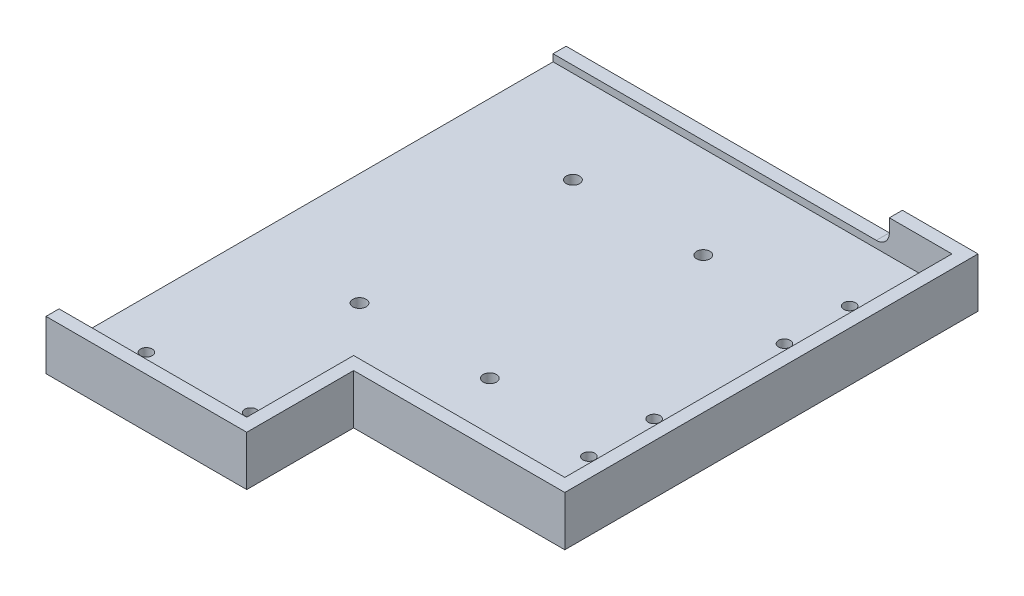
SolidWorks part; units mm, degrees
ref_plane "Front Plane" through (0, 0, 0) normal (0, 0, 1) x (1, 0, 0)
ref_plane "Top Plane" through (0, 0, 0) normal (0, 1, 0) x (1, 0, 0)
ref_plane "Right Plane" through (0, 0, 0) normal (1, 0, 0) x (0, 0, -1)
sketch "Sketch1" plane through (0, 0, 0) normal (0, 1, 0) x (1, 0, 0)
  line L1 (0, 0) -> (158, 0)
  line L2 (0, 0) -> (0, -199.5)
  line L3 (0, -199.5) -> (158, -199.5)
  line L4 (158, 0) -> (158, -199.5)
  dimension "D1" = 158
  dimension "D2" = 199.5
extrude "Boss-Extrude1" add sketch "Sketch1" along normal blind 6.35
sketch "Sketch2" plane through (0, 6.35, 0) normal (0, 1, 0) x (1, 0, 0)
  line L0 (0, -199.5) -> (158, -199.5) construction
  line L1 (158, -199.5) -> (77, -199.5)
  line L2 (158, -199.5) -> (158, -158.5)
  line L3 (158, -158.5) -> (77, -158.5)
  line L4 (77, -199.5) -> (77, -158.5)
  dimension "D1" = 81
  dimension "D2" = 41
extrude "Cut-Extrude1" cut sketch "Sketch2" against normal through all
sketch "Sketch3" plane through (0, 6.35, 0) normal (0, 1, 0) x (1, 0, 0)
  line L0 (0, 0) -> (0, -5)
  line L1 (0, 0) -> (0, -199.5) construction
  line L2 (0, -5) -> (153, -5)
  line L3 (153, -5) -> (153, -153.5)
  line L4 (153, -153.5) -> (72, -153.5)
  line L5 (72, -153.5) -> (72, -194.5)
  line L6 (0, -199.5) -> (77, -199.5) construction
  line L7 (77, -158.5) -> (77, -199.5) construction
  line L8 (158, -158.5) -> (77, -158.5) construction
  line L9 (158, -158.5) -> (158, 0) construction
  line L10 (158, 0) -> (0, 0) construction
  line L11 (77, -158.5) -> (77, -199.5)
  line L12 (158, -158.5) -> (77, -158.5)
  line L13 (158, -158.5) -> (158, 0)
  line L14 (158, 0) -> (0, 0)
  line L15 (72, -199.5) -> (77, -199.5)
  line L17 (0, -194.5) -> (72, -194.5)
  line L18 (0, -194.5) -> (0, -199.5)
  line L19 (0, -199.5) -> (72, -199.5)
  dimension "D1" = 5
  dimension "D2" = 5
  dimension "D3" = 5
  dimension "D4" = 5
  dimension "D5" = 5
extrude "Boss-Extrude2" add sketch "Sketch3" along normal blind 12.7
sketch "Sketch4" plane through (0, 0, 0) normal (0, -1, 0) x (1, 0, 0)
  line L0 (0, 179.5) -> (77, 179.5) construction
  line L1 (0, 0) -> (0, 199.5) construction
  line L2 (77, 158.5) -> (77, 199.5) construction
  line L3 (0, 199.5) -> (77, 199.5) construction
  line L4 (38.5, 179.5) -> (38.5, 188.5903) construction
  line L5 (138, 158.5) -> (138, 0) construction
  line L6 (158, 158.5) -> (77, 158.5) construction
  line L7 (158, 0) -> (0, 0) construction
  line L8 (158, 158.5) -> (158, 0) construction
  line L9 (138, 79.25) -> (152.6176, 79.25) construction
  point P8 (18.5, 179.5)
  point P11 (58.5, 179.5)
  point P20 (138, 129.25)
  point P21 (138, 104.25)
  point P22 (138, 29.25)
  point P23 (138, 79.25)
  point P24 (138, 54.25)
  dimension "D1" = 20
  dimension "D2" = 40
  dimension "D3" = 20
  dimension "D4" = 25
  dimension "D5" = 25
hole_wizard "M4 Clearance Hole1" positions "Sketch4" profile "Sketch5" hole size "M4" standard "ANSI Metric" end condition up to next
sketch "Sketch5" plane through (138, 0, 54.25) normal (1, 0, 0) x (0, 0, -1)
  line L0 (0, 0) -> (0, 6.35)
  line L1 (0, 6.35) -> (2.25, 6.35)
  line L2 (2.25, 6.35) -> (2.25, 0)
  line L5 (2.25, 0) -> (0, 0)
  line L11 (0, -6.35) -> (0, 107.95) construction
  dimension "Thru Hole Dia." = 4.5
  dimension "Thru Hole Depth" = 6.35
sketch "Sketch7" plane through (0, 0, 0) normal (0, 0, -1) x (-1, 0, 0)
  line L0 (-79, 19.05) -> (-79, 4.7647) construction
  line L1 (-158, 19.05) -> (0, 19.05) construction
  line L2 (-158, 19.05) -> (-158, 0) construction
  line L3 (-129, 19.05) -> (0, 19.05)
  line L4 (-129, 19.05) -> (-129, 9.05)
  line L5 (-129, 9.05) -> (0, 9.05)
  line L6 (0, 19.05) -> (0, 9.05)
  line L7 (0, 19.05) -> (0, 0) construction
  dimension "D2" = 10
  dimension "D3" = 29
extrude "Cut-Extrude2" cut sketch "Sketch7" against normal up to next
fillet "Fillet1" radius 5 1 edges at (129, 9.05, 2.5)
sketch "Sketch8" plane through (0, 6.35, 0) normal (0, 1, 0) x (1, 0, 0)
  line L0 (0, -122.25) -> (120.087, -122.25) construction
  line L1 (0, -5) -> (0, -194.5) construction
  line L2 (0, -199.5) -> (77, -199.5) construction
  line L3 (43, -122.25) -> (43, -40.38) construction
  line L4 (93, -122.25) -> (93, -40.38) construction
  point P6 (43, -122.25)
  point P7 (93, -122.25)
  point P13 (93, -40.38)
  point P14 (43, -40.38)
  dimension "D1" = 77.25
  dimension "D2" = 43
  dimension "D3" = 50
  dimension "D4" = 81.87
hole_wizard "Ø5.1 (5.1) Diameter Hole1" positions "Sketch8" profile "Sketch9" hole size "Ø5.1" standard "ANSI Metric" end condition up to next
sketch "Sketch9" plane through (43, 6.35, 40.38) normal (1, 0, 0) x (0, 0, 1)
  line L0 (0, 0) -> (0, 6.35)
  line L1 (0, 6.35) -> (2.55, 6.35)
  line L2 (2.55, 6.35) -> (2.55, 0)
  line L5 (2.55, 0) -> (0, 0)
  line L11 (0, -6.35) -> (0, 107.95) construction
  dimension "Thru Hole Dia." = 5.1
  dimension "Thru Hole Depth" = 6.35
equation "\"D2@Sketch3\"=\"D1@Sketch3\""
equation "\"D3@Sketch3\"=\"D1@Sketch3\""
equation "\"D4@Sketch3\"=\"D1@Sketch3\""
equation "\"D5@Sketch3\"=\"D1@Sketch3\""
